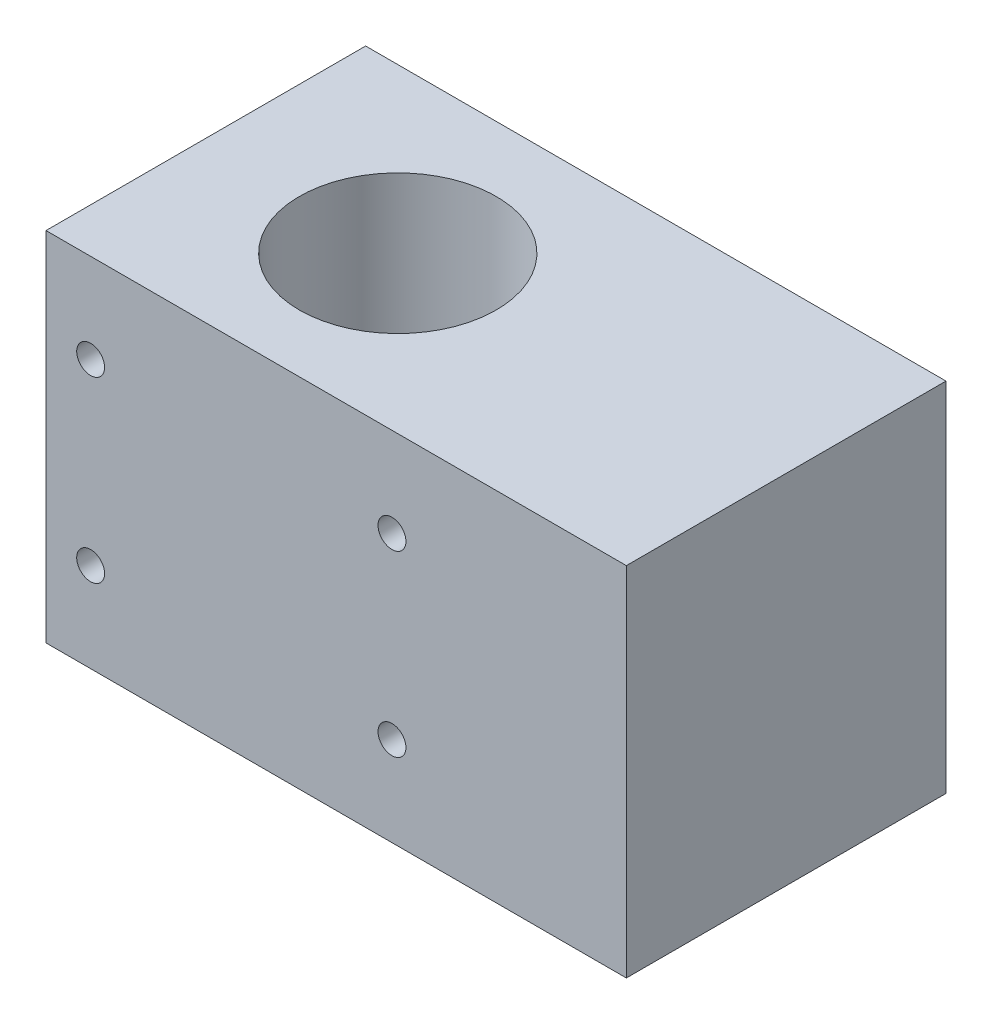
SolidWorks part; units mm, degrees
material "6061 Alloy"
ref_plane "Front Plane" through (0, 0, 0) normal (0, 0, 1) x (1, 0, 0)
ref_plane "Top Plane" through (0, 0, 0) normal (0, 1, 0) x (1, 0, 0)
ref_plane "Right Plane" through (0, 0, 0) normal (1, 0, 0) x (0, 0, -1)
sketch "Sketch1" plane through (0, 0, 0) normal (0, 0, 1) x (1, 0, 0)
  line L0 (0, 0) -> (0, 50.8)
  line L1 (0, 50.8) -> (82.55, 50.8)
  line L2 (55, 0) -> (-55, 0) construction
  line L6 (82.55, 50.8) -> (82.55, 0)
  line L7 (82.55, 0) -> (0, 0)
  point P4 (84.7992, 12.7)
  point P5 (85.725, 62.6195)
  dimension "D1" = 82.55
  dimension "D3" = 50.8
extrude "Boss-Extrude1" add sketch "Sketch1" along normal blind 45.466
sketch "Sketch2" plane through (0, 50.8, 0) normal (0, 1, 0) x (1, 0, 0)
  line L2 (82.55, -45.466) -> (0, -45.466) construction
  line L5 (0, -45.466) -> (0, 0) construction
  circle A0 centre (27.813, -23.241) radius 14
  point P6 (29.8279, -44.45)
  dimension "D1" = 28
  dimension "D2" = 27.813
  dimension "D3" = 22.225
extrude "Cut-Extrude1" cut sketch "Sketch2" against normal through all
hole_wizard "5/32 (0.15625) Diameter Hole1" positions "Sketch5" profile "Sketch6" hole size "5/32" standard "ANSI Inch"
sketch "Sketch5" plane through (0, 0, 45.466) normal (0, 0, 1) x (1, 0, 0)
  line L0 (0, 50.8) -> (0, 0) construction
  line L1 (82.55, 50.8) -> (0, 50.8) construction
  point P0 (6.35, 38.1)
  point P2 (49.2125, 38.1)
  point P4 (49.2125, 12.7)
  point P6 (6.35, 12.7)
  point P9 (0, 0)
  point P10 (0, 0)
  point P11 (0, 0)
  point P12 (0, 0)
  dimension "D1" = 25.4
  dimension "D2" = 42.8625
  dimension "D3" = 6.35
  dimension "D4" = 12.7
sketch "Sketch6" plane through (6.35, 38.1, 45.466) normal (1, 0, 0) x (0, -1, 0)
  line L0 (0, 0) -> (0, 13.8923)
  line L1 (0, 13.8923) -> (1.9844, 12.7)
  line L2 (1.9844, 12.7) -> (1.9844, 0)
  line L5 (1.9844, 0) -> (0, 0)
  line L10 (0, 13.8923) -> (-1.9844, 12.7) construction
  line L11 (0, -6.35) -> (0, 107.95) construction
  dimension "Hole Dia." = 3.9688
  dimension "Hole Depth" = 12.7
  dimension "Drill Angle" = 118
ref_plane "Plane1" through (0, 0, 22.733) normal (0, 0, 1) x (1, 0, 0)
mirror "Mirror1" about plane through (0, 0, 22.733) normal (0, 0, 1) of "5/32 (0.15625) Diameter Hole1"
hole_wizard "Tap Drill for 3/8-24 Tap2" positions "Sketch7" profile "Sketch8" hole size "3/8-24" standard "ANSI Inch"
sketch "Sketch7" plane through (0, 0, 0) normal (0, -1, 0) x (-1, 0, 0)
  line L0 (0, -45.466) -> (-82.55, -45.466) construction
  line L1 (-82.55, -45.466) -> (-82.55, 0) construction
  point P0 (-74.295, -23.241)
  dimension "D1" = 22.225
  dimension "D2" = 8.255
sketch "Sketch8" plane through (74.295, 0, 23.241) normal (1, 0, 0) x (0, 0, -1)
  line L0 (0, 0) -> (0, 34.2835)
  line L1 (0, 34.2835) -> (4.2164, 31.75)
  line L2 (4.2164, 31.75) -> (4.2164, 0)
  line L5 (4.2164, 0) -> (0, 0)
  line L10 (0, 34.2835) -> (-4.2164, 31.75) construction
  line L11 (0, -6.35) -> (0, 107.95) construction
  dimension "Hole Dia." = 8.4328
  dimension "Hole Depth" = 31.75
  dimension "Drill Angle" = 118
